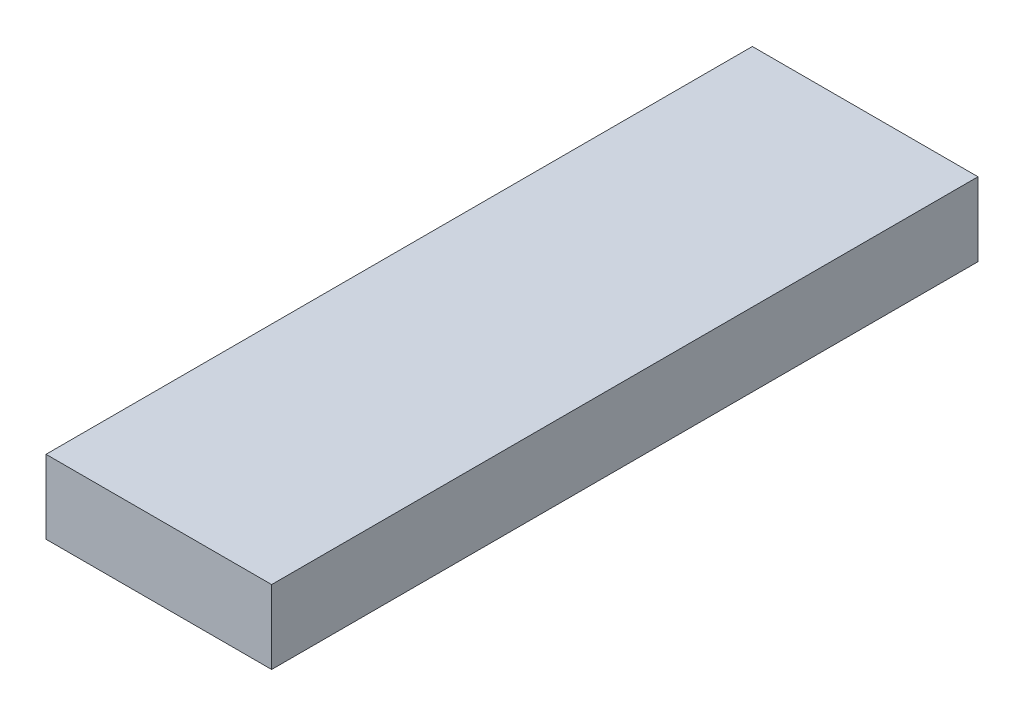
SolidWorks part; units mm, degrees
ref_plane "Front Plane" through (0, 0, 0) normal (0, 0, 1) x (1, 0, 0)
ref_plane "Top Plane" through (0, 0, 0) normal (0, 1, 0) x (1, 0, 0)
ref_plane "Right Plane" through (0, 0, 0) normal (1, 0, 0) x (0, 0, -1)
sketch "Sketch1" plane through (0, 0, 0) normal (0, 1, 0) x (1, 0, 0)
  line L2 (-23, 72) -> (23, 72)
  line L5 (-19, 72) -> (-19, 90)
  line L6 (-19, 90) -> (-4, 90)
  line L7 (-4, 90) -> (-4, 72)
  line L8 (4, 72) -> (4, 90)
  line L9 (4, 90) -> (19, 90)
  line L10 (19, 90) -> (19, 72)
  line L11 (0, 72) -> (0, 180.6197) construction
  line L13 (23, -72) -> (-23, -72)
  line L14 (23, -72) -> (23, 72)
  line L16 (-23, -72) -> (-23, 72)
  line L17 (23, -72) -> (-23, 72) construction
  line L18 (23, 72) -> (-23, -72) construction
  point P0 (0, 0)
  point P16 (-11.5, 90)
  point P17 (11.5, 90)
  dimension "D1" = 144
  dimension "D2" = 46
  dimension "D3" = 15
  dimension "D4" = 23
  dimension "D5" = 18
extrude "cell" add sketch "Sketch1" along normal blind 15 contours L2 L14 L13 L16
equation "\"D1@cell\" = 15.00mm"
